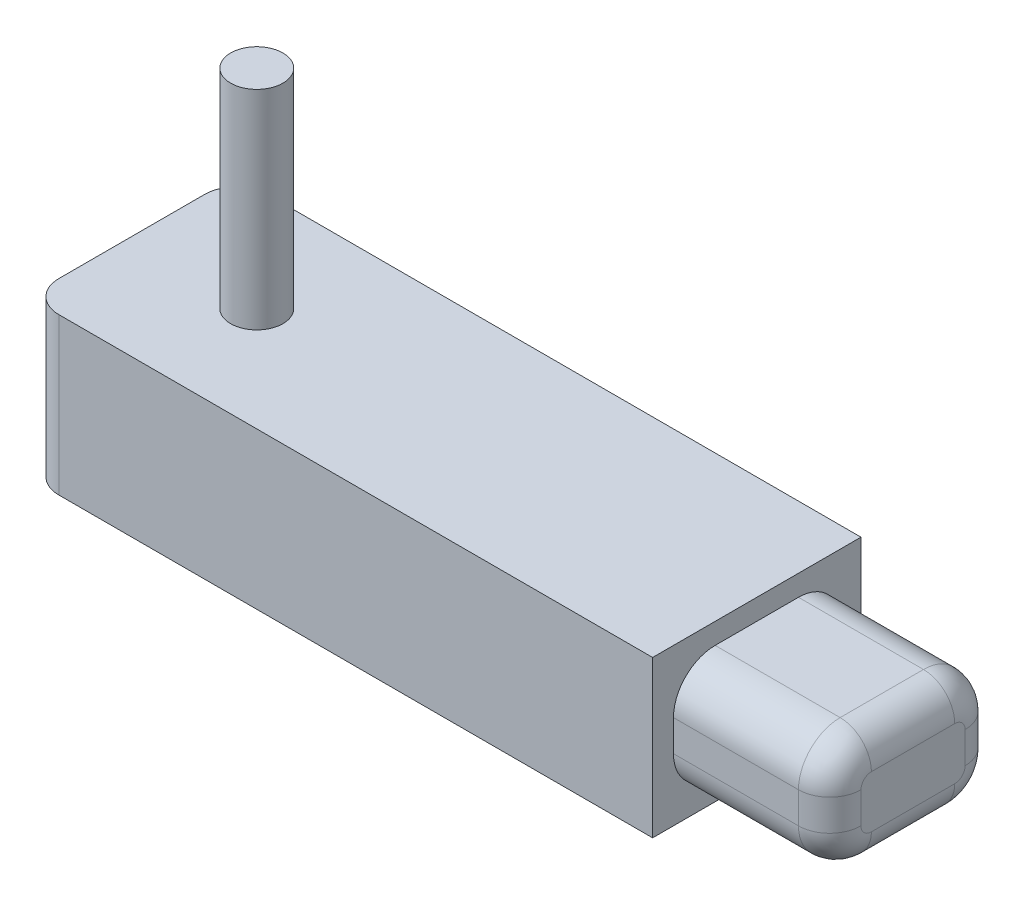
SolidWorks part; units mm, degrees
ref_plane "Front Plane" through (0, 0, 0) normal (0, 0, 1) x (1, 0, 0)
ref_plane "Top Plane" through (0, 0, 0) normal (0, 1, 0) x (1, 0, 0)
ref_plane "Right Plane" through (0, 0, 0) normal (1, 0, 0) x (0, 0, -1)
sketch "Sketch1" plane through (0, 0, 0) normal (0, 0, 1) x (1, 0, 0)
  line L0 (-49.125, 7.0301) -> (10.875, 7.0301)
  line L1 (10.875, 7.0301) -> (10.875, -7.9699)
  line L2 (10.875, -7.9699) -> (-49.125, -7.9699)
  line L3 (-49.125, -7.9699) -> (-49.125, 7.0301)
  dimension "D1" = 15
  dimension "D2" = 15
  dimension "D3" = 60
  dimension "D4" = 60
extrude "Boss-Extrude2" add sketch "Sketch1" along normal blind 20
sketch "Sketch4" plane through (0, 7.0301, 0) normal (0, 1, 0) x (1, 0, 0)
  line L3 (-37.125, -10) -> (-34.6152, -10)
  line L4 (-34.6152, -10) -> (-37.125, -10)
  circle A0 centre (-37.125, -10) radius 2.5098
extrude "Boss-Extrude3" add sketch "Sketch4" along normal blind 20
sketch "Sketch5" plane through (10.875, 0, 0) normal (1, 0, 0) x (0, 0, -1)
  line L0 (-20, -7.9699) -> (-20, 7.0301) construction
  line L1 (-18, -5.9699) -> (-2, -5.9699)
  line L2 (-18, -5.9699) -> (-18, 5.0301)
  line L3 (-18, 5.0301) -> (-2, 5.0301)
  line L4 (-2, -5.9699) -> (-2, 5.0301)
  line L5 (-18, -5.9699) -> (-2, 5.0301) construction
  line L6 (-18, 5.0301) -> (-2, -5.9699) construction
  line L7 (-20, 7.0301) -> (0, 7.0301) construction
  line L8 (0, -7.9699) -> (0, 7.0301) construction
  line L9 (-20, -7.9699) -> (0, -7.9699) construction
  point P0 (-10, -0.4699)
  dimension "D1" = 2
  dimension "D2" = 2
  dimension "D3" = 2
  dimension "D4" = 2
extrude "Boss-Extrude4" add sketch "Sketch5" along normal blind 15
fillet "Fillet2" radius 4 1 edges at (18.375, 5.0301, 2)
fillet "Fillet3" radius 4 1 edges at (18.375, 5.0301, 18)
fillet "Fillet6" radius 4 2 edges at (18.375, -5.9699, 18) (18.375, -5.9699, 2)
fillet "Fillet7" radius 3 8 edges at (25.875, 3.8585, 3.1716) (25.875, -0.4699, 2) (25.875, -4.7983, 3.1716) (25.875, -5.9699, 10) (25.875, -4.7983, 16.8284) (25.875, -0.4699, 18) (25.875, 3.8585, 16.8284) (25.875, 5.0301, 10)
fillet "Fillet8" radius 3 2 edges at (-49.125, -0.4699, 20) (-49.125, -0.4699, 0)
